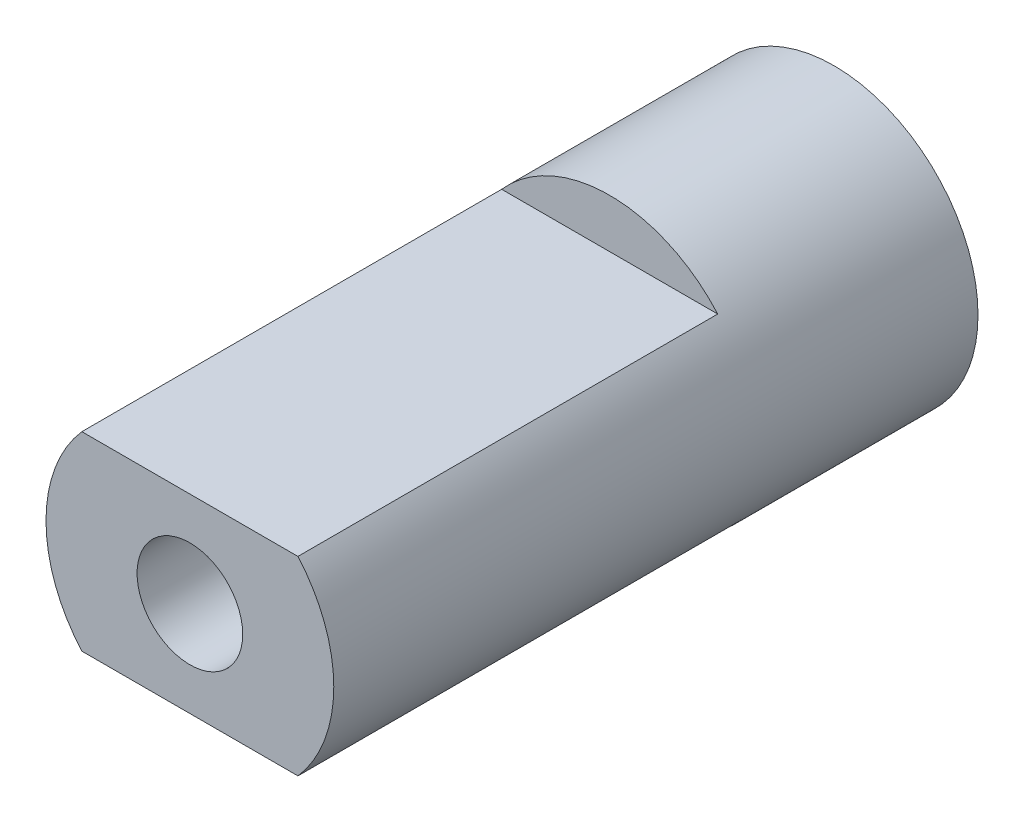
SolidWorks part; units mm, degrees
ref_plane "Front Plane" through (0, 0, 0) normal (0, 0, 1) x (1, 0, 0)
ref_plane "Top Plane" through (0, 0, 0) normal (0, 1, 0) x (1, 0, 0)
ref_plane "Right Plane" through (0, 0, 0) normal (1, 0, 0) x (0, 0, -1)
sketch "Sketch1" plane through (0, 0, 0) normal (0, 0, 1) x (1, 0, 0)
  line L0 (1.6427, 9.0522) -> (1.9304, 8.4575)
  line L1 (0, 9.2) -> (0.3892, 8.6663)
  line L2 (-0.3656, 8.1418) -> (-0.3892, 8.6663)
  line L3 (0, 9.2) -> (-0.3892, 8.6663)
  line L4 (0.3656, 8.1418) -> (0.3892, 8.6663)
  line L5 (1.094, 8.0762) -> (1.1645, 8.5965)
  line L6 (1.6427, 9.0522) -> (1.1645, 8.5965)
  line L7 (1.8135, 7.9457) -> (1.9304, 8.4575)
  line L8 (3.2326, 8.6134) -> (3.4095, 7.9769)
  line L9 (2.5185, 7.7511) -> (2.6807, 8.2504)
  line L10 (3.2326, 8.6134) -> (2.6807, 8.2504)
  line L11 (3.2032, 7.4942) -> (3.4095, 7.9769)
  line L12 (4.7187, 7.8977) -> (4.779, 7.2399)
  line L13 (3.862, 7.1769) -> (4.1108, 7.6392)
  line L14 (4.7187, 7.8977) -> (4.1108, 7.6392)
  line L15 (4.4898, 6.8018) -> (4.779, 7.2399)
  line L16 (6.053, 6.9283) -> (5.995, 6.2702)
  line L17 (5.0814, 6.3719) -> (5.4088, 6.7824)
  line L18 (6.053, 6.9283) -> (5.4088, 6.7824)
  line L19 (5.6322, 5.8908) -> (5.995, 6.2702)
  line L20 (7.1928, 5.7361) -> (7.0182, 5.099)
  line L21 (6.1375, 5.3622) -> (6.5329, 5.7076)
  line L22 (7.1928, 5.7361) -> (6.5329, 5.7076)
  line L23 (6.5935, 4.7904) -> (7.0182, 5.099)
  line L24 (8.1015, 4.3596) -> (7.8159, 3.7639)
  line L25 (6.9964, 4.1801) -> (7.447, 4.4494)
  line L26 (8.1015, 4.3596) -> (7.447, 4.4494)
  line L27 (7.3429, 3.5362) -> (7.8159, 3.7639)
  line L28 (8.7497, 2.843) -> (8.3624, 2.3079)
  line L29 (7.6303, 2.8637) -> (8.1218, 3.0482)
  line L30 (8.7497, 2.843) -> (8.1218, 3.0482)
  line L31 (7.8563, 2.1682) -> (8.3624, 2.3079)
  line L32 (9.1167, 1.2349) -> (8.6401, 0.7776)
  line L33 (8.019, 1.4552) -> (8.5356, 1.549)
  line L34 (9.1167, 1.2349) -> (8.5356, 1.549)
  line L35 (8.1172, 0.7306) -> (8.6401, 0.7776)
  line L36 (9.1907, -0.4128) -> (8.6401, -0.7776)
  line L37 (8.15, 0) -> (8.675, 0)
  line L38 (9.1907, -0.4128) -> (8.675, 0)
  line L39 (8.1172, -0.7306) -> (8.6401, -0.7776)
  line L40 (8.9693, -2.0472) -> (8.3624, -2.3079)
  line L41 (8.019, -1.4552) -> (8.5356, -1.549)
  line L42 (8.9693, -2.0472) -> (8.5356, -1.549)
  line L43 (7.8563, -2.1682) -> (8.3624, -2.3079)
  line L44 (8.4597, -3.6158) -> (7.8159, -3.7639)
  line L45 (7.6303, -2.8637) -> (8.1218, -3.0482)
  line L46 (8.4597, -3.6158) -> (8.1218, -3.0482)
  line L47 (7.3429, -3.5362) -> (7.8159, -3.7639)
  line L48 (7.6781, -5.0683) -> (7.0182, -5.099)
  line L49 (6.9964, -4.1801) -> (7.447, -4.4494)
  line L50 (7.6781, -5.0683) -> (7.447, -4.4494)
  line L51 (6.5935, -4.7904) -> (7.0182, -5.099)
  line L52 (6.6497, -6.3578) -> (5.995, -6.2702)
  line L53 (6.1375, -5.3622) -> (6.5329, -5.7076)
  line L54 (6.6497, -6.3578) -> (6.5329, -5.7076)
  line L55 (5.6322, -5.8908) -> (5.995, -6.2702)
  line L56 (5.4076, -7.443) -> (4.779, -7.2399)
  line L57 (5.0814, -6.3719) -> (5.4088, -6.7824)
  line L58 (5.4076, -7.443) -> (5.4088, -6.7824)
  line L59 (4.4898, -6.8018) -> (4.779, -7.2399)
  line L60 (3.9917, -8.2889) -> (3.4095, -7.9769)
  line L61 (3.862, -7.1769) -> (4.1108, -7.6392)
  line L62 (3.9917, -8.2889) -> (4.1108, -7.6392)
  line L63 (3.2032, -7.4942) -> (3.4095, -7.9769)
  line L64 (2.4475, -8.8685) -> (1.9304, -8.4575)
  line L65 (2.5185, -7.7511) -> (2.6807, -8.2504)
  line L66 (2.4475, -8.8685) -> (2.6807, -8.2504)
  line L67 (1.8135, -7.9457) -> (1.9304, -8.4575)
  line L68 (0.8247, -9.163) -> (0.3892, -8.6663)
  line L69 (1.094, -8.0762) -> (1.1645, -8.5965)
  line L70 (0.8247, -9.163) -> (1.1645, -8.5965)
  line L71 (0.3656, -8.1418) -> (0.3892, -8.6663)
  line L72 (-0.8247, -9.163) -> (-1.1645, -8.5965)
  line L73 (-0.3656, -8.1418) -> (-0.3892, -8.6663)
  line L74 (-0.8247, -9.163) -> (-0.3892, -8.6663)
  line L75 (-1.094, -8.0762) -> (-1.1645, -8.5965)
  line L76 (-2.4475, -8.8685) -> (-2.6807, -8.2504)
  line L77 (-1.8135, -7.9457) -> (-1.9304, -8.4575)
  line L78 (-2.4475, -8.8685) -> (-1.9304, -8.4575)
  line L79 (-2.5185, -7.7511) -> (-2.6807, -8.2504)
  line L80 (-3.9917, -8.2889) -> (-4.1108, -7.6392)
  line L81 (-3.2032, -7.4942) -> (-3.4095, -7.9769)
  line L82 (-3.9917, -8.2889) -> (-3.4095, -7.9769)
  line L83 (-3.862, -7.1769) -> (-4.1108, -7.6392)
  line L84 (-5.4076, -7.443) -> (-5.4088, -6.7824)
  line L85 (-4.4898, -6.8018) -> (-4.779, -7.2399)
  line L86 (-5.4076, -7.443) -> (-4.779, -7.2399)
  line L87 (-5.0814, -6.3719) -> (-5.4088, -6.7824)
  line L88 (-6.6497, -6.3578) -> (-6.5329, -5.7076)
  line L89 (-5.6322, -5.8908) -> (-5.995, -6.2702)
  line L90 (-6.6497, -6.3578) -> (-5.995, -6.2702)
  line L91 (-6.1375, -5.3622) -> (-6.5329, -5.7076)
  line L92 (-7.6781, -5.0683) -> (-7.447, -4.4494)
  line L93 (-6.5935, -4.7904) -> (-7.0182, -5.099)
  line L94 (-7.6781, -5.0683) -> (-7.0182, -5.099)
  line L95 (-6.9964, -4.1801) -> (-7.447, -4.4494)
  line L96 (-8.4597, -3.6158) -> (-8.1218, -3.0482)
  line L97 (-7.3429, -3.5362) -> (-7.8159, -3.7639)
  line L98 (-8.4597, -3.6158) -> (-7.8159, -3.7639)
  line L99 (-7.6303, -2.8637) -> (-8.1218, -3.0482)
  line L100 (-8.9693, -2.0472) -> (-8.5356, -1.549)
  line L101 (-7.8563, -2.1682) -> (-8.3624, -2.3079)
  line L102 (-8.9693, -2.0472) -> (-8.3624, -2.3079)
  line L103 (-8.019, -1.4552) -> (-8.5356, -1.549)
  line L104 (-9.1907, -0.4128) -> (-8.675, 0)
  line L105 (-8.1172, -0.7306) -> (-8.6401, -0.7776)
  line L106 (-9.1907, -0.4128) -> (-8.6401, -0.7776)
  line L107 (-8.15, 0) -> (-8.675, 0)
  line L108 (-9.1167, 1.2349) -> (-8.5356, 1.549)
  line L109 (-8.1172, 0.7306) -> (-8.6401, 0.7776)
  line L110 (-9.1167, 1.2349) -> (-8.6401, 0.7776)
  line L111 (-8.019, 1.4552) -> (-8.5356, 1.549)
  line L112 (-8.7497, 2.843) -> (-8.1218, 3.0482)
  line L113 (-7.8563, 2.1682) -> (-8.3624, 2.3079)
  line L114 (-8.7497, 2.843) -> (-8.3624, 2.3079)
  line L115 (-7.6303, 2.8637) -> (-8.1218, 3.0482)
  line L116 (-8.1015, 4.3596) -> (-7.447, 4.4494)
  line L117 (-7.3429, 3.5362) -> (-7.8159, 3.7639)
  line L118 (-8.1015, 4.3596) -> (-7.8159, 3.7639)
  line L119 (-6.9964, 4.1801) -> (-7.447, 4.4494)
  line L120 (-7.1928, 5.7361) -> (-6.5329, 5.7076)
  line L121 (-6.5935, 4.7904) -> (-7.0182, 5.099)
  line L122 (-7.1928, 5.7361) -> (-7.0182, 5.099)
  line L123 (-6.1375, 5.3622) -> (-6.5329, 5.7076)
  line L124 (-6.053, 6.9283) -> (-5.4088, 6.7824)
  line L125 (-5.6322, 5.8908) -> (-5.995, 6.2702)
  line L126 (-6.053, 6.9283) -> (-5.995, 6.2702)
  line L127 (-5.0814, 6.3719) -> (-5.4088, 6.7824)
  line L128 (-4.7187, 7.8977) -> (-4.1108, 7.6392)
  line L129 (-4.4898, 6.8018) -> (-4.779, 7.2399)
  line L130 (-4.7187, 7.8977) -> (-4.779, 7.2399)
  line L131 (-3.862, 7.1769) -> (-4.1108, 7.6392)
  line L132 (-3.2326, 8.6134) -> (-2.6807, 8.2504)
  line L133 (-3.2032, 7.4942) -> (-3.4095, 7.9769)
  line L134 (-3.2326, 8.6134) -> (-3.4095, 7.9769)
  line L135 (-2.5185, 7.7511) -> (-2.6807, 8.2504)
  line L136 (-1.6427, 9.0522) -> (-1.1645, 8.5965)
  line L137 (-1.8135, 7.9457) -> (-1.9304, 8.4575)
  line L138 (-1.6427, 9.0522) -> (-1.9304, 8.4575)
  line L139 (-1.094, 8.0762) -> (-1.1645, 8.5965)
  arc A0 (0.3656, 8.1418) -> (0.7306, 8.1172) centre (0, 0) cw
  arc A1 (-0.3656, 8.1418) -> (-0.7306, 8.1172) centre (0, 0) ccw
  arc A2 (1.8135, 7.9457) -> (2.1682, 7.8563) centre (0, 0) cw
  arc A3 (1.094, 8.0762) -> (0.7306, 8.1172) centre (0, 0) ccw
  arc A4 (3.2032, 7.4942) -> (3.5362, 7.3429) centre (0, 0) cw
  arc A5 (2.5185, 7.7511) -> (2.1682, 7.8563) centre (0, 0) ccw
  arc A6 (4.4898, 6.8018) -> (4.7904, 6.5935) centre (0, 0) cw
  arc A7 (3.862, 7.1769) -> (3.5362, 7.3429) centre (0, 0) ccw
  arc A8 (5.6322, 5.8908) -> (5.8908, 5.6322) centre (0, 0) cw
  arc A9 (5.0814, 6.3719) -> (4.7904, 6.5935) centre (0, 0) ccw
  arc A10 (6.5935, 4.7904) -> (6.8018, 4.4898) centre (0, 0) cw
  arc A11 (6.1375, 5.3622) -> (5.8908, 5.6322) centre (0, 0) ccw
  arc A12 (7.3429, 3.5362) -> (7.4942, 3.2032) centre (0, 0) cw
  arc A13 (6.9964, 4.1801) -> (6.8018, 4.4898) centre (0, 0) ccw
  arc A14 (7.8563, 2.1682) -> (7.9457, 1.8135) centre (0, 0) cw
  arc A15 (7.6303, 2.8637) -> (7.4942, 3.2032) centre (0, 0) ccw
  arc A16 (8.1172, 0.7306) -> (8.1418, 0.3656) centre (0, 0) cw
  arc A17 (8.019, 1.4552) -> (7.9457, 1.8135) centre (0, 0) ccw
  arc A18 (8.1172, -0.7306) -> (8.0762, -1.094) centre (0, 0) cw
  arc A19 (8.15, 0) -> (8.1418, 0.3656) centre (0, 0) ccw
  arc A20 (7.8563, -2.1682) -> (7.7511, -2.5185) centre (0, 0) cw
  arc A21 (8.019, -1.4552) -> (8.0762, -1.094) centre (0, 0) ccw
  arc A22 (7.3429, -3.5362) -> (7.1769, -3.862) centre (0, 0) cw
  arc A23 (7.6303, -2.8637) -> (7.7511, -2.5185) centre (0, 0) ccw
  arc A24 (6.5935, -4.7904) -> (6.3719, -5.0814) centre (0, 0) cw
  arc A25 (6.9964, -4.1801) -> (7.1769, -3.862) centre (0, 0) ccw
  arc A26 (5.6322, -5.8908) -> (5.3622, -6.1375) centre (0, 0) cw
  arc A27 (6.1375, -5.3622) -> (6.3719, -5.0814) centre (0, 0) ccw
  arc A28 (4.4898, -6.8018) -> (4.1801, -6.9964) centre (0, 0) cw
  arc A29 (5.0814, -6.3719) -> (5.3622, -6.1375) centre (0, 0) ccw
  arc A30 (3.2032, -7.4942) -> (2.8637, -7.6303) centre (0, 0) cw
  arc A31 (3.862, -7.1769) -> (4.1801, -6.9964) centre (0, 0) ccw
  arc A32 (1.8135, -7.9457) -> (1.4552, -8.019) centre (0, 0) cw
  arc A33 (2.5185, -7.7511) -> (2.8637, -7.6303) centre (0, 0) ccw
  arc A34 (0.3656, -8.1418) -> (0, -8.15) centre (0, 0) cw
  arc A35 (1.094, -8.0762) -> (1.4552, -8.019) centre (0, 0) ccw
  arc A36 (-1.094, -8.0762) -> (-1.4552, -8.019) centre (0, 0) cw
  arc A37 (-0.3656, -8.1418) -> (0, -8.15) centre (0, 0) ccw
  arc A38 (-2.5185, -7.7511) -> (-2.8637, -7.6303) centre (0, 0) cw
  arc A39 (-1.8135, -7.9457) -> (-1.4552, -8.019) centre (0, 0) ccw
  arc A40 (-3.862, -7.1769) -> (-4.1801, -6.9964) centre (0, 0) cw
  arc A41 (-3.2032, -7.4942) -> (-2.8637, -7.6303) centre (0, 0) ccw
  arc A42 (-5.0814, -6.3719) -> (-5.3622, -6.1375) centre (0, 0) cw
  arc A43 (-4.4898, -6.8018) -> (-4.1801, -6.9964) centre (0, 0) ccw
  arc A44 (-6.1375, -5.3622) -> (-6.3719, -5.0814) centre (0, 0) cw
  arc A45 (-5.6322, -5.8908) -> (-5.3622, -6.1375) centre (0, 0) ccw
  arc A46 (-6.9964, -4.1801) -> (-7.1769, -3.862) centre (0, 0) cw
  arc A47 (-6.5935, -4.7904) -> (-6.3719, -5.0814) centre (0, 0) ccw
  arc A48 (-7.6303, -2.8637) -> (-7.7511, -2.5185) centre (0, 0) cw
  arc A49 (-7.3429, -3.5362) -> (-7.1769, -3.862) centre (0, 0) ccw
  arc A50 (-8.019, -1.4552) -> (-8.0762, -1.094) centre (0, 0) cw
  arc A51 (-7.8563, -2.1682) -> (-7.7511, -2.5185) centre (0, 0) ccw
  arc A52 (-8.15, 0) -> (-8.1418, 0.3656) centre (0, 0) cw
  arc A53 (-8.1172, -0.7306) -> (-8.0762, -1.094) centre (0, 0) ccw
  arc A54 (-8.019, 1.4552) -> (-7.9457, 1.8135) centre (0, 0) cw
  arc A55 (-8.1172, 0.7306) -> (-8.1418, 0.3656) centre (0, 0) ccw
  arc A56 (-7.6303, 2.8637) -> (-7.4942, 3.2032) centre (0, 0) cw
  arc A57 (-7.8563, 2.1682) -> (-7.9457, 1.8135) centre (0, 0) ccw
  arc A58 (-6.9964, 4.1801) -> (-6.8018, 4.4898) centre (0, 0) cw
  arc A59 (-7.3429, 3.5362) -> (-7.4942, 3.2032) centre (0, 0) ccw
  arc A60 (-6.1375, 5.3622) -> (-5.8908, 5.6322) centre (0, 0) cw
  arc A61 (-6.5935, 4.7904) -> (-6.8018, 4.4898) centre (0, 0) ccw
  arc A62 (-5.0814, 6.3719) -> (-4.7904, 6.5935) centre (0, 0) cw
  arc A63 (-5.6322, 5.8908) -> (-5.8908, 5.6322) centre (0, 0) ccw
  arc A64 (-3.862, 7.1769) -> (-3.5362, 7.3429) centre (0, 0) cw
  arc A65 (-4.4898, 6.8018) -> (-4.7904, 6.5935) centre (0, 0) ccw
  arc A66 (-2.5185, 7.7511) -> (-2.1682, 7.8563) centre (0, 0) cw
  arc A67 (-3.2032, 7.4942) -> (-3.5362, 7.3429) centre (0, 0) ccw
  arc A68 (-1.094, 8.0762) -> (-0.7306, 8.1172) centre (0, 0) cw
  arc A69 (-1.8135, 7.9457) -> (-2.1682, 7.8563) centre (0, 0) ccw
  circle A70 centre (0, 0) radius 1
  point P250 (0, 0)
  dimension "D1" = 35
  dimension "D2" = 16.3
  dimension "D3" = 2
extrude "Boss-Extrude1" add sketch "Sketch1" along normal blind 3
sketch "Sketch2" plane through (0, 0, 0) normal (0, 0, -1) x (-1, 0, 0)
  circle A0 centre (0, 0) radius 1.75
  circle A1 centre (0, 0) radius 1 construction
  circle A2 centre (0, 0) radius 1
  dimension "D1" = 3.5
extrude "Boss-Extrude2" add sketch "Sketch2" along normal blind 0.5
sketch "Sketch3" plane through (0, 0, 3) normal (0, 0, 1) x (1, 0, 0)
  circle A0 centre (0, 0) radius 2.725
  circle A2 centre (0, 0) radius 1
  dimension "D1" = 5.45
extrude "Boss-Extrude3" add sketch "Sketch3" along normal blind 10.3
sketch "Sketch4" plane through (0, 0, 13.3) normal (0, 0, 1) x (1, 0, 0)
  line L1 (-2.0459, -1.8) -> (2.0459, -1.8)
  line L3 (-2.0459, 1.8) -> (2.0459, 1.8)
  circle A0 centre (0, 0) radius 2.725 construction
  arc A1 (2.0459, 1.8) -> (-2.0459, 1.8) centre (0, 0) ccw
  arc A2 (-2.0459, -1.8) -> (2.0459, -1.8) centre (0, 0) ccw
  point P0 (0, 0)
extrude "Cut-Extrude1" cut sketch "Sketch4" against normal blind 7.95
sketch "Sketch6" plane through (0, 0, -0.5) normal (0, 0, -1) x (-1, 0, 0)
  line L140 (0.3656, 8.1418) -> (0.3892, 8.6663)
  line L141 (0.3892, 8.6663) -> (0, 9.2)
  line L142 (0, 9.2) -> (-0.3892, 8.6663)
  line L143 (-0.3892, 8.6663) -> (-0.3656, 8.1418)
  line L144 (-1.094, 8.0762) -> (-1.1645, 8.5965)
  line L145 (-1.1645, 8.5965) -> (-1.6427, 9.0522)
  line L146 (-1.6427, 9.0522) -> (-1.9304, 8.4575)
  line L147 (-1.9304, 8.4575) -> (-1.8135, 7.9457)
  line L148 (-2.5185, 7.7511) -> (-2.6807, 8.2504)
  line L149 (-2.6807, 8.2504) -> (-3.2326, 8.6134)
  line L150 (-3.2326, 8.6134) -> (-3.4095, 7.9769)
  line L151 (-3.4095, 7.9769) -> (-3.2032, 7.4942)
  line L152 (-3.862, 7.1769) -> (-4.1108, 7.6392)
  line L153 (-4.1108, 7.6392) -> (-4.7187, 7.8977)
  line L154 (-4.7187, 7.8977) -> (-4.779, 7.2399)
  line L155 (-4.779, 7.2399) -> (-4.4898, 6.8018)
  line L156 (-5.0814, 6.3719) -> (-5.4088, 6.7824)
  line L157 (-5.4088, 6.7824) -> (-6.053, 6.9283)
  line L158 (-6.053, 6.9283) -> (-5.995, 6.2702)
  line L159 (-5.995, 6.2702) -> (-5.6322, 5.8908)
  line L160 (-6.1375, 5.3622) -> (-6.5329, 5.7076)
  line L161 (-6.5329, 5.7076) -> (-7.1928, 5.7361)
  line L162 (-7.1928, 5.7361) -> (-7.0182, 5.099)
  line L163 (-7.0182, 5.099) -> (-6.5935, 4.7904)
  line L164 (-6.9964, 4.1801) -> (-7.447, 4.4494)
  line L165 (-7.447, 4.4494) -> (-8.1015, 4.3596)
  line L166 (-8.1015, 4.3596) -> (-7.8159, 3.7639)
  line L167 (-7.8159, 3.7639) -> (-7.3429, 3.5362)
  line L168 (-7.6303, 2.8637) -> (-8.1218, 3.0482)
  line L169 (-8.1218, 3.0482) -> (-8.7497, 2.843)
  line L170 (-8.7497, 2.843) -> (-8.3624, 2.3079)
  line L171 (-8.3624, 2.3079) -> (-7.8563, 2.1682)
  line L172 (-8.019, 1.4552) -> (-8.5356, 1.549)
  line L173 (-8.5356, 1.549) -> (-9.1167, 1.2349)
  line L174 (-9.1167, 1.2349) -> (-8.6401, 0.7776)
  line L175 (-8.6401, 0.7776) -> (-8.1172, 0.7306)
  line L176 (-8.15, 0) -> (-8.675, 0)
  line L177 (-8.675, 0) -> (-9.1907, -0.4128)
  line L178 (-9.1907, -0.4128) -> (-8.6401, -0.7776)
  line L179 (-8.6401, -0.7776) -> (-8.1172, -0.7306)
  line L180 (-8.019, -1.4552) -> (-8.5356, -1.549)
  line L181 (-8.5356, -1.549) -> (-8.9693, -2.0472)
  line L182 (-8.9693, -2.0472) -> (-8.3624, -2.3079)
  line L183 (-8.3624, -2.3079) -> (-7.8563, -2.1682)
  line L184 (-7.6303, -2.8637) -> (-8.1218, -3.0482)
  line L185 (-8.1218, -3.0482) -> (-8.4597, -3.6158)
  line L186 (-8.4597, -3.6158) -> (-7.8159, -3.7639)
  line L187 (-7.8159, -3.7639) -> (-7.3429, -3.5362)
  line L188 (-6.9964, -4.1801) -> (-7.447, -4.4494)
  line L189 (-7.447, -4.4494) -> (-7.6781, -5.0683)
  line L190 (-7.6781, -5.0683) -> (-7.0182, -5.099)
  line L191 (-7.0182, -5.099) -> (-6.5935, -4.7904)
  line L192 (-6.1375, -5.3622) -> (-6.5329, -5.7076)
  line L193 (-6.5329, -5.7076) -> (-6.6497, -6.3578)
  line L194 (-6.6497, -6.3578) -> (-5.995, -6.2702)
  line L195 (-5.995, -6.2702) -> (-5.6322, -5.8908)
  line L196 (-5.0814, -6.3719) -> (-5.4088, -6.7824)
  line L197 (-5.4088, -6.7824) -> (-5.4076, -7.443)
  line L198 (-5.4076, -7.443) -> (-4.779, -7.2399)
  line L199 (-4.779, -7.2399) -> (-4.4898, -6.8018)
  line L200 (-3.862, -7.1769) -> (-4.1108, -7.6392)
  line L201 (-4.1108, -7.6392) -> (-3.9917, -8.2889)
  line L202 (-3.9917, -8.2889) -> (-3.4095, -7.9769)
  line L203 (-3.4095, -7.9769) -> (-3.2032, -7.4942)
  line L204 (-2.5185, -7.7511) -> (-2.6807, -8.2504)
  line L205 (-2.6807, -8.2504) -> (-2.4475, -8.8685)
  line L206 (-2.4475, -8.8685) -> (-1.9304, -8.4575)
  line L207 (-1.9304, -8.4575) -> (-1.8135, -7.9457)
  line L208 (-1.094, -8.0762) -> (-1.1645, -8.5965)
  line L209 (-1.1645, -8.5965) -> (-0.8247, -9.163)
  line L210 (-0.8247, -9.163) -> (-0.3892, -8.6663)
  line L211 (-0.3892, -8.6663) -> (-0.3656, -8.1418)
  line L212 (0.3656, -8.1418) -> (0.3892, -8.6663)
  line L213 (0.3892, -8.6663) -> (0.8247, -9.163)
  line L214 (0.8247, -9.163) -> (1.1645, -8.5965)
  line L215 (1.1645, -8.5965) -> (1.094, -8.0762)
  line L216 (1.8135, -7.9457) -> (1.9304, -8.4575)
  line L217 (1.9304, -8.4575) -> (2.4475, -8.8685)
  line L218 (2.4475, -8.8685) -> (2.6807, -8.2504)
  line L219 (2.6807, -8.2504) -> (2.5185, -7.7511)
  line L220 (3.2032, -7.4942) -> (3.4095, -7.9769)
  line L221 (3.4095, -7.9769) -> (3.9917, -8.2889)
  line L222 (3.9917, -8.2889) -> (4.1108, -7.6392)
  line L223 (4.1108, -7.6392) -> (3.862, -7.1769)
  line L224 (4.4898, -6.8018) -> (4.779, -7.2399)
  line L225 (4.779, -7.2399) -> (5.4076, -7.443)
  line L226 (5.4076, -7.443) -> (5.4088, -6.7824)
  line L227 (5.4088, -6.7824) -> (5.0814, -6.3719)
  line L228 (5.6322, -5.8908) -> (5.995, -6.2702)
  line L229 (5.995, -6.2702) -> (6.6497, -6.3578)
  line L230 (6.6497, -6.3578) -> (6.5329, -5.7076)
  line L231 (6.5329, -5.7076) -> (6.1375, -5.3622)
  line L232 (6.5935, -4.7904) -> (7.0182, -5.099)
  line L233 (7.0182, -5.099) -> (7.6781, -5.0683)
  line L234 (7.6781, -5.0683) -> (7.447, -4.4494)
  line L235 (7.447, -4.4494) -> (6.9964, -4.1801)
  line L236 (7.3429, -3.5362) -> (7.8159, -3.7639)
  line L237 (7.8159, -3.7639) -> (8.4597, -3.6158)
  line L238 (8.4597, -3.6158) -> (8.1218, -3.0482)
  line L239 (8.1218, -3.0482) -> (7.6303, -2.8637)
  line L240 (7.8563, -2.1682) -> (8.3624, -2.3079)
  line L241 (8.3624, -2.3079) -> (8.9693, -2.0472)
  line L242 (8.9693, -2.0472) -> (8.5356, -1.549)
  line L243 (8.5356, -1.549) -> (8.019, -1.4552)
  line L244 (8.1172, -0.7306) -> (8.6401, -0.7776)
  line L245 (8.6401, -0.7776) -> (9.1907, -0.4128)
  line L246 (9.1907, -0.4128) -> (8.675, 0)
  line L247 (8.675, 0) -> (8.15, 0)
  line L248 (8.1172, 0.7306) -> (8.6401, 0.7776)
  line L249 (8.6401, 0.7776) -> (9.1167, 1.2349)
  line L250 (9.1167, 1.2349) -> (8.5356, 1.549)
  line L251 (8.5356, 1.549) -> (8.019, 1.4552)
  line L252 (7.8563, 2.1682) -> (8.3624, 2.3079)
  line L253 (8.3624, 2.3079) -> (8.7497, 2.843)
  line L254 (8.7497, 2.843) -> (8.1218, 3.0482)
  line L255 (8.1218, 3.0482) -> (7.6303, 2.8637)
  line L256 (7.3429, 3.5362) -> (7.8159, 3.7639)
  line L257 (7.8159, 3.7639) -> (8.1015, 4.3596)
  line L258 (8.1015, 4.3596) -> (7.447, 4.4494)
  line L259 (7.447, 4.4494) -> (6.9964, 4.1801)
  line L260 (6.5935, 4.7904) -> (7.0182, 5.099)
  line L261 (7.0182, 5.099) -> (7.1928, 5.7361)
  line L262 (7.1928, 5.7361) -> (6.5329, 5.7076)
  line L263 (6.5329, 5.7076) -> (6.1375, 5.3622)
  line L264 (5.6322, 5.8908) -> (5.995, 6.2702)
  line L265 (5.995, 6.2702) -> (6.053, 6.9283)
  line L266 (6.053, 6.9283) -> (5.4088, 6.7824)
  line L267 (5.4088, 6.7824) -> (5.0814, 6.3719)
  line L268 (4.4898, 6.8018) -> (4.779, 7.2399)
  line L269 (4.779, 7.2399) -> (4.7187, 7.8977)
  line L270 (4.7187, 7.8977) -> (4.1108, 7.6392)
  line L271 (4.1108, 7.6392) -> (3.862, 7.1769)
  line L272 (3.2032, 7.4942) -> (3.4095, 7.9769)
  line L273 (3.4095, 7.9769) -> (3.2326, 8.6134)
  line L274 (3.2326, 8.6134) -> (2.6807, 8.2504)
  line L275 (2.6807, 8.2504) -> (2.5185, 7.7511)
  line L276 (1.8135, 7.9457) -> (1.9304, 8.4575)
  line L277 (1.9304, 8.4575) -> (1.6427, 9.0522)
  line L278 (1.6427, 9.0522) -> (1.1645, 8.5965)
  line L279 (1.1645, 8.5965) -> (1.094, 8.0762)
  line L280 (0.3656, 8.1418) -> (0.3892, 8.6663)
  line L281 (0.3892, 8.6663) -> (0, 9.2)
  line L282 (0, 9.2) -> (-0.3892, 8.6663)
  line L283 (-0.3892, 8.6663) -> (-0.3656, 8.1418)
  line L284 (-1.094, 8.0762) -> (-1.1645, 8.5965)
  line L285 (-1.1645, 8.5965) -> (-1.6427, 9.0522)
  line L286 (-1.6427, 9.0522) -> (-1.9304, 8.4575)
  line L287 (-1.9304, 8.4575) -> (-1.8135, 7.9457)
  line L288 (-2.5185, 7.7511) -> (-2.6807, 8.2504)
  line L289 (-2.6807, 8.2504) -> (-3.2326, 8.6134)
  line L290 (-3.2326, 8.6134) -> (-3.4095, 7.9769)
  line L291 (-3.4095, 7.9769) -> (-3.2032, 7.4942)
  line L292 (-3.862, 7.1769) -> (-4.1108, 7.6392)
  line L293 (-4.1108, 7.6392) -> (-4.7187, 7.8977)
  line L294 (-4.7187, 7.8977) -> (-4.779, 7.2399)
  line L295 (-4.779, 7.2399) -> (-4.4898, 6.8018)
  line L296 (-5.0814, 6.3719) -> (-5.4088, 6.7824)
  line L297 (-5.4088, 6.7824) -> (-6.053, 6.9283)
  line L298 (-6.053, 6.9283) -> (-5.995, 6.2702)
  line L299 (-5.995, 6.2702) -> (-5.6322, 5.8908)
  line L300 (-6.1375, 5.3622) -> (-6.5329, 5.7076)
  line L301 (-6.5329, 5.7076) -> (-7.1928, 5.7361)
  line L302 (-7.1928, 5.7361) -> (-7.0182, 5.099)
  line L303 (-7.0182, 5.099) -> (-6.5935, 4.7904)
  line L304 (-6.9964, 4.1801) -> (-7.447, 4.4494)
  line L305 (-7.447, 4.4494) -> (-8.1015, 4.3596)
  line L306 (-8.1015, 4.3596) -> (-7.8159, 3.7639)
  line L307 (-7.8159, 3.7639) -> (-7.3429, 3.5362)
  line L308 (-7.6303, 2.8637) -> (-8.1218, 3.0482)
  line L309 (-8.1218, 3.0482) -> (-8.7497, 2.843)
  line L310 (-8.7497, 2.843) -> (-8.3624, 2.3079)
  line L311 (-8.3624, 2.3079) -> (-7.8563, 2.1682)
  line L312 (-8.019, 1.4552) -> (-8.5356, 1.549)
  line L313 (-8.5356, 1.549) -> (-9.1167, 1.2349)
  line L314 (-9.1167, 1.2349) -> (-8.6401, 0.7776)
  line L315 (-8.6401, 0.7776) -> (-8.1172, 0.7306)
  line L316 (-8.15, 0) -> (-8.675, 0)
  line L317 (-8.675, 0) -> (-9.1907, -0.4128)
  line L318 (-9.1907, -0.4128) -> (-8.6401, -0.7776)
  line L319 (-8.6401, -0.7776) -> (-8.1172, -0.7306)
  line L320 (-8.019, -1.4552) -> (-8.5356, -1.549)
  line L321 (-8.5356, -1.549) -> (-8.9693, -2.0472)
  line L322 (-8.9693, -2.0472) -> (-8.3624, -2.3079)
  line L323 (-8.3624, -2.3079) -> (-7.8563, -2.1682)
  line L324 (-7.6303, -2.8637) -> (-8.1218, -3.0482)
  line L325 (-8.1218, -3.0482) -> (-8.4597, -3.6158)
  line L326 (-8.4597, -3.6158) -> (-7.8159, -3.7639)
  line L327 (-7.8159, -3.7639) -> (-7.3429, -3.5362)
  line L328 (-6.9964, -4.1801) -> (-7.447, -4.4494)
  line L329 (-7.447, -4.4494) -> (-7.6781, -5.0683)
  line L330 (-7.6781, -5.0683) -> (-7.0182, -5.099)
  line L331 (-7.0182, -5.099) -> (-6.5935, -4.7904)
  line L332 (-6.1375, -5.3622) -> (-6.5329, -5.7076)
  line L333 (-6.5329, -5.7076) -> (-6.6497, -6.3578)
  line L334 (-6.6497, -6.3578) -> (-5.995, -6.2702)
  line L335 (-5.995, -6.2702) -> (-5.6322, -5.8908)
  line L336 (-5.0814, -6.3719) -> (-5.4088, -6.7824)
  line L337 (-5.4088, -6.7824) -> (-5.4076, -7.443)
  line L338 (-5.4076, -7.443) -> (-4.779, -7.2399)
  line L339 (-4.779, -7.2399) -> (-4.4898, -6.8018)
  line L340 (-3.862, -7.1769) -> (-4.1108, -7.6392)
  line L341 (-4.1108, -7.6392) -> (-3.9917, -8.2889)
  line L342 (-3.9917, -8.2889) -> (-3.4095, -7.9769)
  line L343 (-3.4095, -7.9769) -> (-3.2032, -7.4942)
  line L344 (-2.5185, -7.7511) -> (-2.6807, -8.2504)
  line L345 (-2.6807, -8.2504) -> (-2.4475, -8.8685)
  line L346 (-2.4475, -8.8685) -> (-1.9304, -8.4575)
  line L347 (-1.9304, -8.4575) -> (-1.8135, -7.9457)
  line L348 (-1.094, -8.0762) -> (-1.1645, -8.5965)
  line L349 (-1.1645, -8.5965) -> (-0.8247, -9.163)
  line L350 (-0.8247, -9.163) -> (-0.3892, -8.6663)
  line L351 (-0.3892, -8.6663) -> (-0.3656, -8.1418)
  line L352 (0.3656, -8.1418) -> (0.3892, -8.6663)
  line L353 (0.3892, -8.6663) -> (0.8247, -9.163)
  line L354 (0.8247, -9.163) -> (1.1645, -8.5965)
  line L355 (1.1645, -8.5965) -> (1.094, -8.0762)
  line L356 (1.8135, -7.9457) -> (1.9304, -8.4575)
  line L357 (1.9304, -8.4575) -> (2.4475, -8.8685)
  line L358 (2.4475, -8.8685) -> (2.6807, -8.2504)
  line L359 (2.6807, -8.2504) -> (2.5185, -7.7511)
  line L360 (3.2032, -7.4942) -> (3.4095, -7.9769)
  line L361 (3.4095, -7.9769) -> (3.9917, -8.2889)
  line L362 (3.9917, -8.2889) -> (4.1108, -7.6392)
  line L363 (4.1108, -7.6392) -> (3.862, -7.1769)
  line L364 (4.4898, -6.8018) -> (4.779, -7.2399)
  line L365 (4.779, -7.2399) -> (5.4076, -7.443)
  line L366 (5.4076, -7.443) -> (5.4088, -6.7824)
  line L367 (5.4088, -6.7824) -> (5.0814, -6.3719)
  line L368 (5.6322, -5.8908) -> (5.995, -6.2702)
  line L369 (5.995, -6.2702) -> (6.6497, -6.3578)
  line L370 (6.6497, -6.3578) -> (6.5329, -5.7076)
  line L371 (6.5329, -5.7076) -> (6.1375, -5.3622)
  line L372 (6.5935, -4.7904) -> (7.0182, -5.099)
  line L373 (7.0182, -5.099) -> (7.6781, -5.0683)
  line L374 (7.6781, -5.0683) -> (7.447, -4.4494)
  line L375 (7.447, -4.4494) -> (6.9964, -4.1801)
  line L376 (7.3429, -3.5362) -> (7.8159, -3.7639)
  line L377 (7.8159, -3.7639) -> (8.4597, -3.6158)
  line L378 (8.4597, -3.6158) -> (8.1218, -3.0482)
  line L379 (8.1218, -3.0482) -> (7.6303, -2.8637)
  line L380 (7.8563, -2.1682) -> (8.3624, -2.3079)
  line L381 (8.3624, -2.3079) -> (8.9693, -2.0472)
  line L382 (8.9693, -2.0472) -> (8.5356, -1.549)
  line L383 (8.5356, -1.549) -> (8.019, -1.4552)
  line L384 (8.1172, -0.7306) -> (8.6401, -0.7776)
  line L385 (8.6401, -0.7776) -> (9.1907, -0.4128)
  line L386 (9.1907, -0.4128) -> (8.675, 0)
  line L387 (8.675, 0) -> (8.15, 0)
  line L388 (8.1172, 0.7306) -> (8.6401, 0.7776)
  line L389 (8.6401, 0.7776) -> (9.1167, 1.2349)
  line L390 (9.1167, 1.2349) -> (8.5356, 1.549)
  line L391 (8.5356, 1.549) -> (8.019, 1.4552)
  line L392 (7.8563, 2.1682) -> (8.3624, 2.3079)
  line L393 (8.3624, 2.3079) -> (8.7497, 2.843)
  line L394 (8.7497, 2.843) -> (8.1218, 3.0482)
  line L395 (8.1218, 3.0482) -> (7.6303, 2.8637)
  line L396 (7.3429, 3.5362) -> (7.8159, 3.7639)
  line L397 (7.8159, 3.7639) -> (8.1015, 4.3596)
  line L398 (8.1015, 4.3596) -> (7.447, 4.4494)
  line L399 (7.447, 4.4494) -> (6.9964, 4.1801)
  line L400 (6.5935, 4.7904) -> (7.0182, 5.099)
  line L401 (7.0182, 5.099) -> (7.1928, 5.7361)
  line L402 (7.1928, 5.7361) -> (6.5329, 5.7076)
  line L403 (6.5329, 5.7076) -> (6.1375, 5.3622)
  line L404 (5.6322, 5.8908) -> (5.995, 6.2702)
  line L405 (5.995, 6.2702) -> (6.053, 6.9283)
  line L406 (6.053, 6.9283) -> (5.4088, 6.7824)
  line L407 (5.4088, 6.7824) -> (5.0814, 6.3719)
  line L408 (4.4898, 6.8018) -> (4.779, 7.2399)
  line L409 (4.779, 7.2399) -> (4.7187, 7.8977)
  line L410 (4.7187, 7.8977) -> (4.1108, 7.6392)
  line L411 (4.1108, 7.6392) -> (3.862, 7.1769)
  line L412 (3.2032, 7.4942) -> (3.4095, 7.9769)
  line L413 (3.4095, 7.9769) -> (3.2326, 8.6134)
  line L414 (3.2326, 8.6134) -> (2.6807, 8.2504)
  line L415 (2.6807, 8.2504) -> (2.5185, 7.7511)
  line L416 (1.8135, 7.9457) -> (1.9304, 8.4575)
  line L417 (1.9304, 8.4575) -> (1.6427, 9.0522)
  line L418 (1.6427, 9.0522) -> (1.1645, 8.5965)
  line L419 (1.1645, 8.5965) -> (1.094, 8.0762)
  arc A35 (1.094, 8.0762) -> (0.3656, 8.1418) centre (0, 0) ccw
  arc A36 (-0.3656, 8.1418) -> (-1.094, 8.0762) centre (0, 0) ccw
  arc A37 (-1.8135, 7.9457) -> (-2.5185, 7.7511) centre (0, 0) ccw
  arc A38 (-3.2032, 7.4942) -> (-3.862, 7.1769) centre (0, 0) ccw
  arc A39 (-4.4898, 6.8018) -> (-5.0814, 6.3719) centre (0, 0) ccw
  arc A40 (-5.6322, 5.8908) -> (-6.1375, 5.3622) centre (0, 0) ccw
  arc A41 (-6.5935, 4.7904) -> (-6.9964, 4.1801) centre (0, 0) ccw
  arc A42 (-7.3429, 3.5362) -> (-7.6303, 2.8637) centre (0, 0) ccw
  arc A43 (-7.8563, 2.1682) -> (-8.019, 1.4552) centre (0, 0) ccw
  arc A44 (-8.1172, 0.7306) -> (-8.15, 0) centre (0, 0) ccw
  arc A45 (-8.1172, -0.7306) -> (-8.019, -1.4552) centre (0, 0) ccw
  arc A46 (-7.8563, -2.1682) -> (-7.6303, -2.8637) centre (0, 0) ccw
  arc A47 (-7.3429, -3.5362) -> (-6.9964, -4.1801) centre (0, 0) ccw
  arc A48 (-6.5935, -4.7904) -> (-6.1375, -5.3622) centre (0, 0) ccw
  arc A49 (-5.6322, -5.8908) -> (-5.0814, -6.3719) centre (0, 0) ccw
  arc A50 (-4.4898, -6.8018) -> (-3.862, -7.1769) centre (0, 0) ccw
  arc A51 (-3.2032, -7.4942) -> (-2.5185, -7.7511) centre (0, 0) ccw
  arc A52 (-1.8135, -7.9457) -> (-1.094, -8.0762) centre (0, 0) ccw
  arc A53 (-0.3656, -8.1418) -> (0.3656, -8.1418) centre (0, 0) ccw
  arc A54 (1.094, -8.0762) -> (1.8135, -7.9457) centre (0, 0) ccw
  arc A55 (2.5185, -7.7511) -> (3.2032, -7.4942) centre (0, 0) ccw
  arc A56 (3.862, -7.1769) -> (4.4898, -6.8018) centre (0, 0) ccw
  arc A57 (5.0814, -6.3719) -> (5.6322, -5.8908) centre (0, 0) ccw
  arc A58 (6.1375, -5.3622) -> (6.5935, -4.7904) centre (0, 0) ccw
  arc A59 (6.9964, -4.1801) -> (7.3429, -3.5362) centre (0, 0) ccw
  arc A60 (7.6303, -2.8637) -> (7.8563, -2.1682) centre (0, 0) ccw
  arc A61 (8.019, -1.4552) -> (8.1172, -0.7306) centre (0, 0) ccw
  arc A62 (8.15, 0) -> (8.1172, 0.7306) centre (0, 0) ccw
  arc A63 (8.019, 1.4552) -> (7.8563, 2.1682) centre (0, 0) ccw
  arc A64 (7.6303, 2.8637) -> (7.3429, 3.5362) centre (0, 0) ccw
  arc A65 (6.9964, 4.1801) -> (6.5935, 4.7904) centre (0, 0) ccw
  arc A66 (6.1375, 5.3622) -> (5.6322, 5.8908) centre (0, 0) ccw
  arc A67 (5.0814, 6.3719) -> (4.4898, 6.8018) centre (0, 0) ccw
  arc A68 (3.862, 7.1769) -> (3.2032, 7.4942) centre (0, 0) ccw
  arc A69 (2.5185, 7.7511) -> (1.8135, 7.9457) centre (0, 0) ccw
  arc A70 (1.094, 8.0762) -> (0.3656, 8.1418) centre (0, 0) ccw
  arc A71 (-0.3656, 8.1418) -> (-1.094, 8.0762) centre (0, 0) ccw
  arc A72 (-1.8135, 7.9457) -> (-2.5185, 7.7511) centre (0, 0) ccw
  arc A73 (-3.2032, 7.4942) -> (-3.862, 7.1769) centre (0, 0) ccw
  arc A74 (-4.4898, 6.8018) -> (-5.0814, 6.3719) centre (0, 0) ccw
  arc A75 (-5.6322, 5.8908) -> (-6.1375, 5.3622) centre (0, 0) ccw
  arc A76 (-6.5935, 4.7904) -> (-6.9964, 4.1801) centre (0, 0) ccw
  arc A77 (-7.3429, 3.5362) -> (-7.6303, 2.8637) centre (0, 0) ccw
  arc A78 (-7.8563, 2.1682) -> (-8.019, 1.4552) centre (0, 0) ccw
  arc A79 (-8.1172, 0.7306) -> (-8.15, 0) centre (0, 0) ccw
  arc A80 (-8.1172, -0.7306) -> (-8.019, -1.4552) centre (0, 0) ccw
  arc A81 (-7.8563, -2.1682) -> (-7.6303, -2.8637) centre (0, 0) ccw
  arc A82 (-7.3429, -3.5362) -> (-6.9964, -4.1801) centre (0, 0) ccw
  arc A83 (-6.5935, -4.7904) -> (-6.1375, -5.3622) centre (0, 0) ccw
  arc A84 (-5.6322, -5.8908) -> (-5.0814, -6.3719) centre (0, 0) ccw
  arc A85 (-4.4898, -6.8018) -> (-3.862, -7.1769) centre (0, 0) ccw
  arc A86 (-3.2032, -7.4942) -> (-2.5185, -7.7511) centre (0, 0) ccw
  arc A87 (-1.8135, -7.9457) -> (-1.094, -8.0762) centre (0, 0) ccw
  arc A88 (-0.3656, -8.1418) -> (0.3656, -8.1418) centre (0, 0) ccw
  arc A89 (1.094, -8.0762) -> (1.8135, -7.9457) centre (0, 0) ccw
  arc A90 (2.5185, -7.7511) -> (3.2032, -7.4942) centre (0, 0) ccw
  arc A91 (3.862, -7.1769) -> (4.4898, -6.8018) centre (0, 0) ccw
  arc A92 (5.0814, -6.3719) -> (5.6322, -5.8908) centre (0, 0) ccw
  arc A93 (6.1375, -5.3622) -> (6.5935, -4.7904) centre (0, 0) ccw
  arc A94 (6.9964, -4.1801) -> (7.3429, -3.5362) centre (0, 0) ccw
  arc A95 (7.6303, -2.8637) -> (7.8563, -2.1682) centre (0, 0) ccw
  arc A96 (8.019, -1.4552) -> (8.1172, -0.7306) centre (0, 0) ccw
  arc A97 (8.15, 0) -> (8.1172, 0.7306) centre (0, 0) ccw
  arc A98 (8.019, 1.4552) -> (7.8563, 2.1682) centre (0, 0) ccw
  arc A99 (7.6303, 2.8637) -> (7.3429, 3.5362) centre (0, 0) ccw
  arc A100 (6.9964, 4.1801) -> (6.5935, 4.7904) centre (0, 0) ccw
  arc A101 (6.1375, 5.3622) -> (5.6322, 5.8908) centre (0, 0) ccw
  arc A102 (5.0814, 6.3719) -> (4.4898, 6.8018) centre (0, 0) ccw
  arc A103 (3.862, 7.1769) -> (3.2032, 7.4942) centre (0, 0) ccw
  arc A104 (2.5185, 7.7511) -> (1.8135, 7.9457) centre (0, 0) ccw
  dimension "D1" = 0
extrude "Cut-Extrude3" cut sketch "Sketch6" against normal up to vertex (3.5 mm away)
sketch "Sketch8" plane through (0, 0, 13.3) normal (0, 0, 1) x (1, 0, 0)
  line L1 (2.0459, -1.8) -> (-2.0459, -1.8)
  line L2 (2.0459, -1.8) -> (-2.0459, -1.8)
  arc A1 (-2.0459, -1.8) -> (2.0459, -1.8) centre (0, 0) ccw
  arc A2 (-2.0459, -1.8) -> (2.0459, -1.8) centre (0, 0) ccw
  dimension "D1" = 0
extrude "Cut-Extrude4" cut sketch "Sketch8" against normal blind 8.4
sketch "Sketch9" plane through (0, 0, 13.3) normal (0, 0, 1) x (1, 0, 0)
  line L2 (2.0459, 1.8) -> (-2.0459, 1.8)
  line L3 (-2.0459, -1.8) -> (2.0459, -1.8)
  line L4 (2.0459, 1.8) -> (-2.0459, 1.8)
  line L5 (-2.0459, -1.8) -> (2.0459, -1.8)
  circle A0 centre (0, 0) radius 1 construction
  circle A1 centre (0, 0) radius 1
  arc A2 (-2.0459, 1.8) -> (-2.0459, -1.8) centre (0, 0) ccw
  arc A3 (2.0459, -1.8) -> (2.0459, 1.8) centre (0, 0) ccw
  arc A4 (-2.0459, 1.8) -> (-2.0459, -1.8) centre (0, 0) ccw
  arc A5 (2.0459, -1.8) -> (2.0459, 1.8) centre (0, 0) ccw
  dimension "D1" = 0
extrude "Boss-Extrude4" add sketch "Sketch9" against normal blind 12.2
sketch "Sketch10" plane through (0, 0, 3) normal (0, 0, -1) x (-1, 0, 0)
  line L1 (2.0459, -1.8) -> (-2.0459, -1.8)
  line L2 (2.0459, -1.8) -> (-2.0459, -1.8)
  line L3 (-2.0459, 1.8) -> (2.0459, 1.8)
  line L4 (-2.0459, 1.8) -> (2.0459, 1.8)
  arc A1 (-2.0459, -1.8) -> (2.0459, -1.8) centre (0, 0) ccw
  arc A2 (-2.0459, -1.8) -> (2.0459, -1.8) centre (0, 0) ccw
  arc A3 (2.0459, 1.8) -> (-2.0459, 1.8) centre (0, 0) ccw
  arc A4 (2.0459, 1.8) -> (-2.0459, 1.8) centre (0, 0) ccw
  dimension "D1" = 0
  dimension "D2" = 0
extrude "Boss-Extrude5" add sketch "Sketch10" along normal up to vertex
ref_plane "Plane1" through (0, 0, 7.4) normal (0, 0, 1) x (1, 0, 0)
